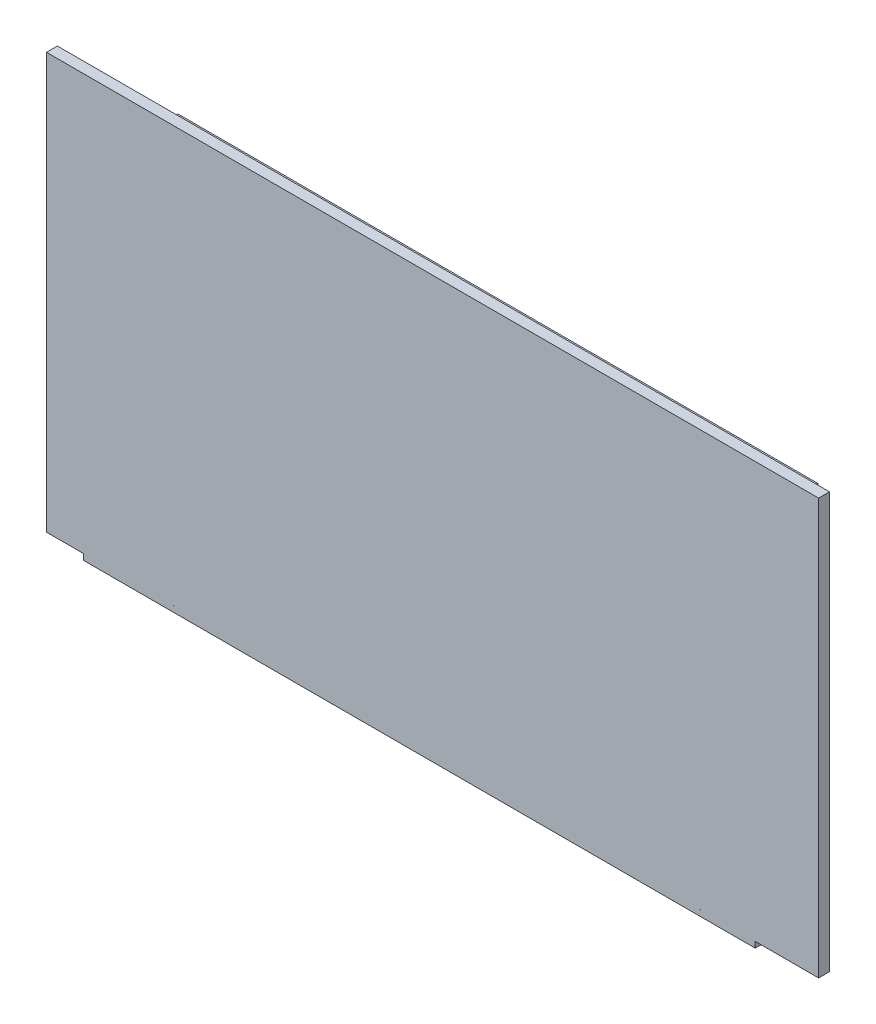
SolidWorks part; units mm, degrees
ref_plane "Plano frontal" through (0, 0, 0) normal (0, 0, 1) x (1, 0, 0)
ref_plane "Plano superior" through (0, 0, 0) normal (0, 1, 0) x (1, 0, 0)
ref_plane "Plano direito" through (0, 0, 0) normal (1, 0, 0) x (0, 0, -1)
sketch "Esboço1" plane through (0, 0, 0) normal (0, 0, 1) x (1, 0, 0)
  line L1 (-52.5, 30) -> (52.5, 30)
  line L2 (-52.5, 30) -> (-52.5, -30)
  line L3 (-52.5, -30) -> (52.5, -30)
  line L4 (52.5, 30) -> (52.5, -30)
  line L5 (-52.5, 30) -> (52.5, -30) construction
  line L6 (-52.5, -30) -> (52.5, 30) construction
  point P0 (0, 0)
  dimension "D1" = 60
  dimension "D2" = 105
extrude "Ressalto-extrusão1" add sketch "Esboço1" along normal blind 1.7
sketch "Esboço3" plane through (0, 0, 0) normal (0, 0, -1) x (-1, 0, 0)
  line L0 (52.5, -30) -> (-52.5, -30) construction
  line L1 (52.5, 30.9) -> (-47.5, 30.9)
  line L2 (52.5, 30.9) -> (52.5, -22.1)
  line L3 (52.5, -22.1) -> (-47.5, -22.1)
  line L4 (-47.5, 30.9) -> (-47.5, -22.1)
  line L5 (52.5, 30) -> (52.5, -30) construction
  dimension "D1" = 7.9
  dimension "D2" = 53
  dimension "D3" = 100
extrude "Ressalto-extrusão6" add sketch "Esboço3" along normal blind 1.5 from offset 11.6 separate body
sketch "Esboço4" plane through (0, 0, -11.6) normal (0, 0, 1) x (1, 0, 0)
  line L1 (-23.9415, 27.9898) -> (38.2426, 27.9898)
  line L2 (-23.9415, 27.9898) -> (-23.9415, 25.4498)
  line L3 (-23.9415, 25.4498) -> (38.2426, 25.4498)
  line L4 (38.2426, 27.9898) -> (38.2426, 25.4498)
  line L5 (48.3249, 26.9052) -> (43.2449, 26.9052)
  line L6 (48.3249, 26.9052) -> (48.3249, -16.0526)
  line L7 (48.3249, -16.0526) -> (43.2449, -16.0526)
  line L8 (43.2449, 26.9052) -> (43.2449, -16.0526)
  line L9 (38.2426, -19.9599) -> (-17.8292, -19.9599)
  line L10 (38.2426, -19.9599) -> (38.2426, -17.4199)
  line L11 (38.2426, -17.4199) -> (-17.8292, -17.4199)
  line L12 (-17.8292, -19.9599) -> (-17.8292, -17.4199)
  dimension "D1" = 2.54
  dimension "D2" = 5.08
extrude "Ressalto-extrusão8" add sketch "Esboço4" along normal up to surface (11.6 mm away) up to face at (0, 0, 0)
sketch "Esboço7" plane through (0, 0, -11.6) normal (0, 0, 1) x (1, 0, 0)
  line L0 (-52.5, 30.9) -> (47.5, 30.9) construction
  line L1 (-34.753, 23.9) -> (-60.5, 23.9)
  line L2 (-34.753, 23.9) -> (-34.753, 11.9)
  line L3 (-34.753, 11.9) -> (-60.5, 11.9)
  line L4 (-60.5, 23.9) -> (-60.5, 11.9)
  line L5 (-52.5, -22.1) -> (-52.5, 30.9) construction
  dimension "D1" = 7
  dimension "D2" = 12
  dimension "D3" = 8
extrude "Ressalto-extrusão10" add sketch "Esboço7" along normal blind 10
sketch "Esboço8" plane through (0, 0, -13.1) normal (0, 0, -1) x (-1, 0, 0)
  line L0 (52.5, -22.1) -> (52.5, 30.9) construction
  line L1 (-47.5, -22.1) -> (52.5, -22.1) construction
  line L3 (-52.5, -30) -> (52.5, -30)
  line L4 (-52.5, -30) -> (-52.5, -22.1)
  line L5 (-52.5, -22.1) -> (52.5, -22.1)
  line L6 (52.5, -30) -> (52.5, -22.1)
  circle A0 centre (37.26, 28.47) radius 1.5
  circle A1 centre (38.5, -19.7) radius 1.5
  circle A2 centre (-43.8, -19.7) radius 1.5
  dimension "D1" = 3
  dimension "D2" = 15.24
  dimension "D3" = 14
  dimension "D4" = 82.3
  dimension "D5" = 2.4
  dimension "D6" = 2.4
  dimension "D7" = 48.17
extrude "Corte-extrusão1" cut sketch "Esboço8" against normal through all
sketch "Esboço9" plane through (0, 0, 1.7) normal (0, 0, 1) x (1, 0, 0)
  line L1 (-58.2592, 43.7736) -> (62.4118, 43.7736)
  line L2 (-58.2592, 43.7736) -> (-58.2592, -21.1797)
  line L3 (-58.2592, -21.1797) -> (62.4118, -21.1797)
  line L4 (62.4118, 43.7736) -> (62.4118, -21.1797)
  line L5 (-58.2592, 43.7736) -> (62.4118, -21.1797) construction
  line L6 (-58.2592, -21.1797) -> (62.4118, 43.7736) construction
  point P0 (2.0763, 11.2969)
  point P5 (2.8494, 1.0456)
  point P6 (56.9299, -33.1419)
  point P7 (57.8829, 39.7596)
  point P8 (74.6235, -22.2295)
  point P9 (54.5204, -21.1797)
  point P10 (62.4118, 43.7736)
extrude "Ressalto-extrusão11" add sketch "Esboço9" against normal up to surface (1.7 mm away) up to face at (45.3, -19.7, 0)
equation "\"D2@Esboço4\"=\"D1@Esboço4\"*2"
